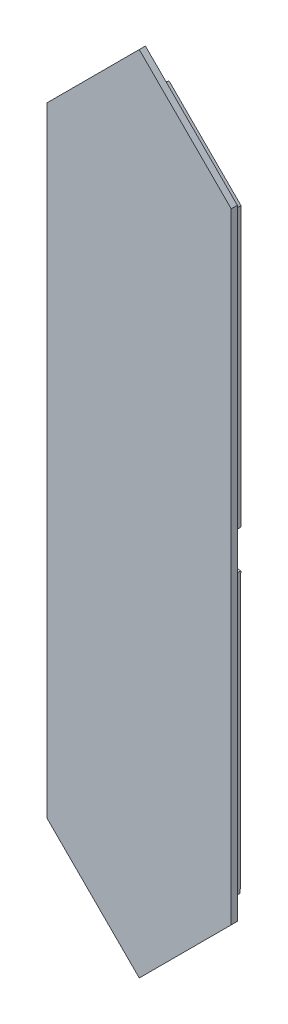
SolidWorks part; units mm, degrees
ref_plane "Plan de face" through (0, 0, 0) normal (0, 0, 1) x (1, 0, 0)
ref_plane "Plan de dessus" through (0, 0, 0) normal (0, 1, 0) x (1, 0, 0)
ref_plane "Plan de droite" through (0, 0, 0) normal (1, 0, 0) x (0, 0, -1)
sketch "Esquisse1" plane through (0, 0, 0) normal (0, 0, 1) x (1, 0, 0)
  line L8 (-13.1868, -48.8132) -> (-1.8385, -60.1615)
  line L9 (1.8385, -60.1615) -> (13.4433, -48.5999)
  line L10 (13.5707, 48.4293) -> (1.8385, 60.1615)
  line L11 (-1.8385, 60.1615) -> (-13.1033, 48.9831)
  line L12 (-13.1033, -3.0745) -> (-13.1868, -48.8132)
  line L13 (13.4433, -48.5999) -> (13.5263, -3.0999)
  line L14 (13.5707, 3.0992) -> (13.5707, 48.4293)
  line L15 (-13.1033, 48.9831) -> (-13.1033, 3.0745)
  arc A4 (1.8385, -60.1615) -> (-1.8385, -60.1615) centre (0, -62) ccw
  arc A5 (-1.8385, 60.1615) -> (1.8385, 60.1615) centre (0, 62) ccw
  arc A6 (13.5707, 3.0992) -> (13.5263, -3.0999) centre (13.5, 0) ccw
  arc A7 (-13.1033, -3.0745) -> (-13.1033, 3.0745) centre (-13.5, 0) ccw
  point P20 (0, 0)
  dimension "D1" = 62
  dimension "D2" = 62
  dimension "D3" = 3.1
  dimension "D4" = 3.1
  dimension "D5" = 2.6
  dimension "D6" = 2.6
extrude "Boss.-Extru.1" add sketch "Esquisse1" along normal blind 2
sketch "Esquisse2" plane through (0, 0, 2) normal (0, 0, 1) x (1, 0, 0)
  line L0 (0, 65.1513) -> (-15.0282, 50.1231)
  line L1 (-15.0282, 50.1231) -> (-15.0282, -50.7526)
  line L2 (-15.0282, -50.7526) -> (0, -65.7808)
  line L3 (0, -82.4436) -> (0, 83.024) construction
  line L4 (0, 65.1513) -> (14.9718, 50.1794)
  line L5 (14.9718, 50.1794) -> (14.9718, -50.8089)
  line L6 (14.9718, -50.8089) -> (0, -65.7808)
  dimension "D1" = 130.932
  dimension "D2" = 30
extrude "Boss.-Extru.2" add sketch "Esquisse2" along normal blind 1
